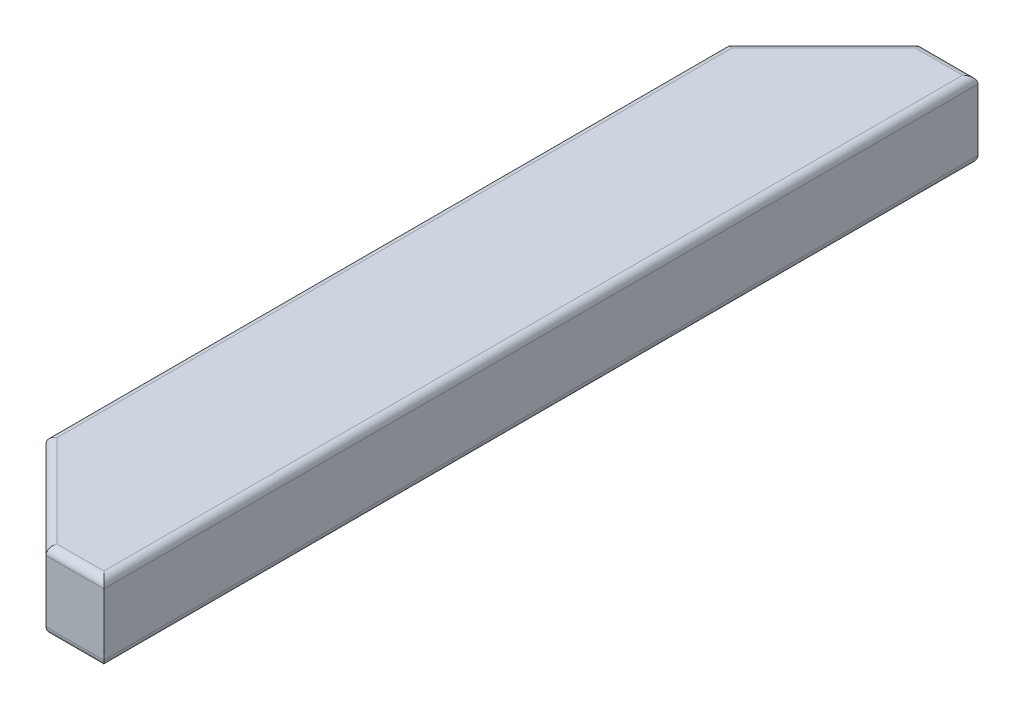
SolidWorks part; units mm, degrees
material "Balsa"
ref_plane "Front Plane" through (0, 0, 0) normal (0, 0, 1) x (1, 0, 0)
ref_plane "Top Plane" through (0, 0, 0) normal (0, 1, 0) x (1, 0, 0)
ref_plane "Right Plane" through (0, 0, 0) normal (1, 0, 0) x (0, 0, -1)
sketch "Sketch2" plane through (0, 0, 287.7) normal (0, 0, -1) x (-1, 0, 0)
  line L0 (-316.47, -12.7) -> (316.47, -12.7) construction
  line L5 (-2714.3, 38.1) -> (-2612.7, 38.1)
  line L6 (-2714.3, 38.1) -> (-2714.3, -12.7)
  line L7 (-2714.3, -12.7) -> (-2612.7, -12.7)
  line L8 (-2612.7, 38.1) -> (-2612.7, -12.7)
  line L9 (-1812.7, 38.1) -> (-2714.3, 38.1) construction
extrude "Boss-Extrude1" add sketch "Sketch2" along normal up to surface (575.4 mm away)
sketch "Sketch5" plane through (0, 38.1, 0) normal (0, 1, 0) x (1, 0, 0)
  line L1 (2714.3, 0) -> (2612.7, 0) construction
  line L2 (2714.3, 287.7) -> (2714.3, -287.7) construction
  line L5 (2612.7, 287.7) -> (2612.7, -287.7) construction
  line L15 (2612.7, -287.7) -> (2676.2, -287.7)
  line L16 (2676.2, -287.7) -> (2612.7, -224.2)
  line L17 (2612.7, -224.2) -> (2612.7, -287.7)
  line L18 (2676.2, 287.7) -> (2612.7, 224.2)
  line L19 (2612.7, 287.7) -> (2676.2, 287.7)
  line L20 (2612.7, 224.2) -> (2612.7, 287.7)
  line L21 (2663.5, 287.7) -> (2663.5, -287.7) construction
  line L22 (2714.3, 287.7) -> (2612.7, 287.7) construction
  line L23 (2612.7, -287.7) -> (2714.3, -287.7) construction
  point P0 (2612.7, 219.8497)
  point P19 (0, 0)
  point P20 (0, 0)
  point P21 (0, 0)
  point P22 (0, 0)
  dimension "D1" = 63.5
  dimension "D2" = 45
extrude "Cut-Extrude1" cut sketch "Sketch5" against normal through all
fillet "Fillet1" radius 5.08 12 edges at (2612.7, -12.7, 0) (2612.7, 38.1, 0) (2714.3, -12.7, 0) (2714.3, 38.1, 0) (2695.25, -12.7, 287.7) (2644.45, -12.7, 255.95) (2695.25, 38.1, 287.7) (2644.45, 38.1, 255.95) (2695.25, -12.7, -287.7) (2695.25, 38.1, -287.7) (2644.45, -12.7, -255.95) (2644.45, 38.1, -255.95)
